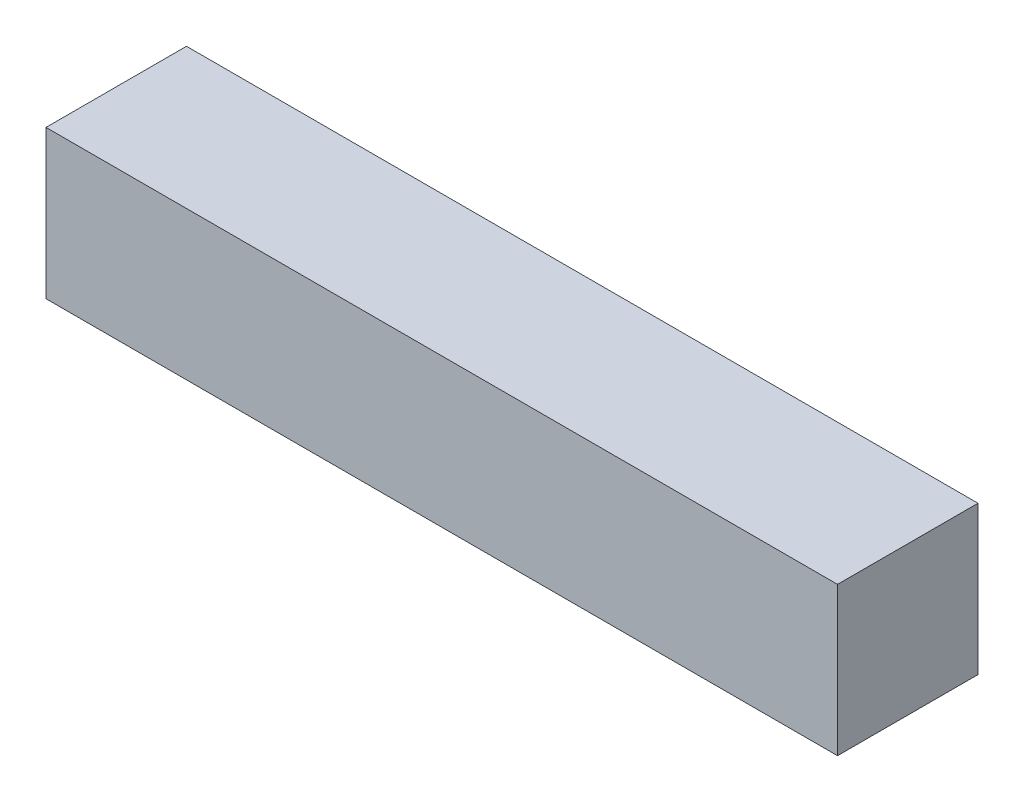
SolidWorks part; units mm, degrees
material "Balsa"
ref_plane "Front Plane" through (0, 0, 0) normal (0, 0, 1) x (1, 0, 0)
ref_plane "Top Plane" through (0, 0, 0) normal (0, 1, 0) x (1, 0, 0)
ref_plane "Right Plane" through (0, 0, 0) normal (1, 0, 0) x (0, 0, -1)
sketch "Sketch2" plane through (0, 0, 0) normal (0, 1, 0) x (1, 0, 0)
  line L1 (-101.6, -18.034) -> (101.6, -18.034)
  line L2 (-101.6, -18.034) -> (-101.6, 18.034)
  line L3 (-101.6, 18.034) -> (101.6, 18.034)
  line L4 (101.6, -18.034) -> (101.6, 18.034)
  line L5 (-101.6, -18.034) -> (101.6, 18.034) construction
  line L6 (-101.6, 18.034) -> (101.6, -18.034) construction
  point P0 (0, 0)
  dimension "D1" = 203.2
  dimension "D2" = 36.068
extrude "Boss-Extrude1" add sketch "Sketch2" along normal blind 38.1 contours L3 L4 L1 L2
